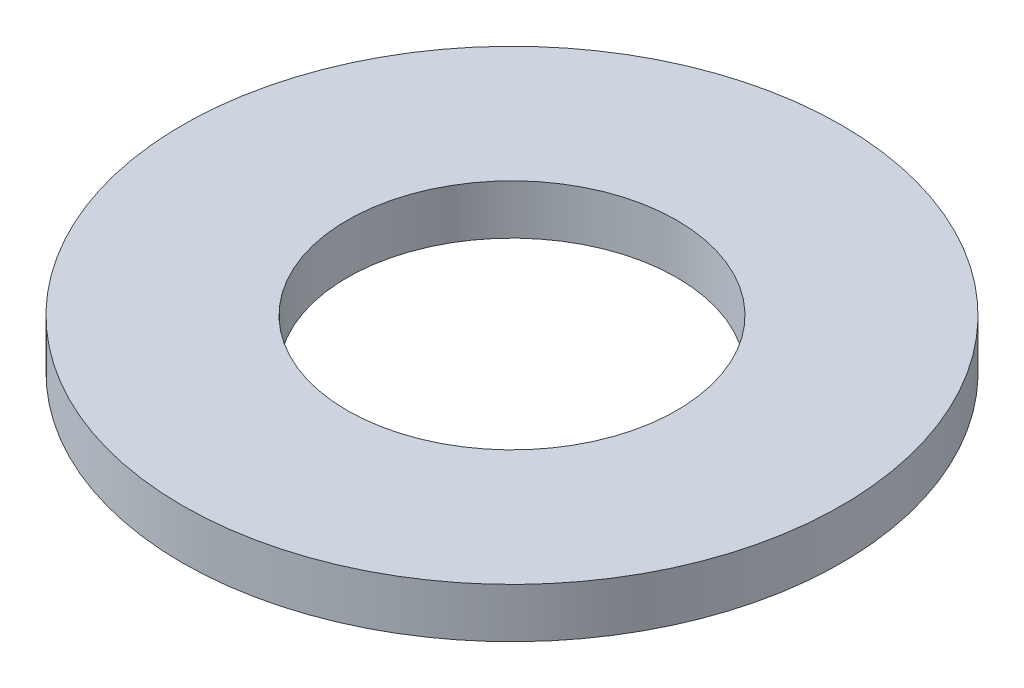
SolidWorks part; units mm, degrees
material "Plain Carbon Steel"
ref_plane "Front Plane" through (0, 0, 0) normal (0, 0, 1) x (1, 0, 0)
ref_plane "Top Plane" through (0, 0, 0) normal (0, 1, 0) x (1, 0, 0)
ref_plane "Right Plane" through (0, 0, 0) normal (1, 0, 0) x (0, 0, -1)
sketch "Sketch1" plane through (0, 0, 0) normal (0, 1, 0) x (1, 0, 0)
  circle A0 centre (0, 0) radius 13.4938
  dimension "OD" = 26.9875
extrude "Boss-Extrude1" add sketch "Sketch1" along normal blind 2.032
sketch "Sketch5" plane through (0, 2.032, 0) normal (0, 1, 0) x (-1, 0, 0)
  circle A0 centre (0, 0) radius 6.7469
  dimension "ID" = 13.4937
extrude "Cut-Extrude1" cut sketch "Sketch5" against normal through all
